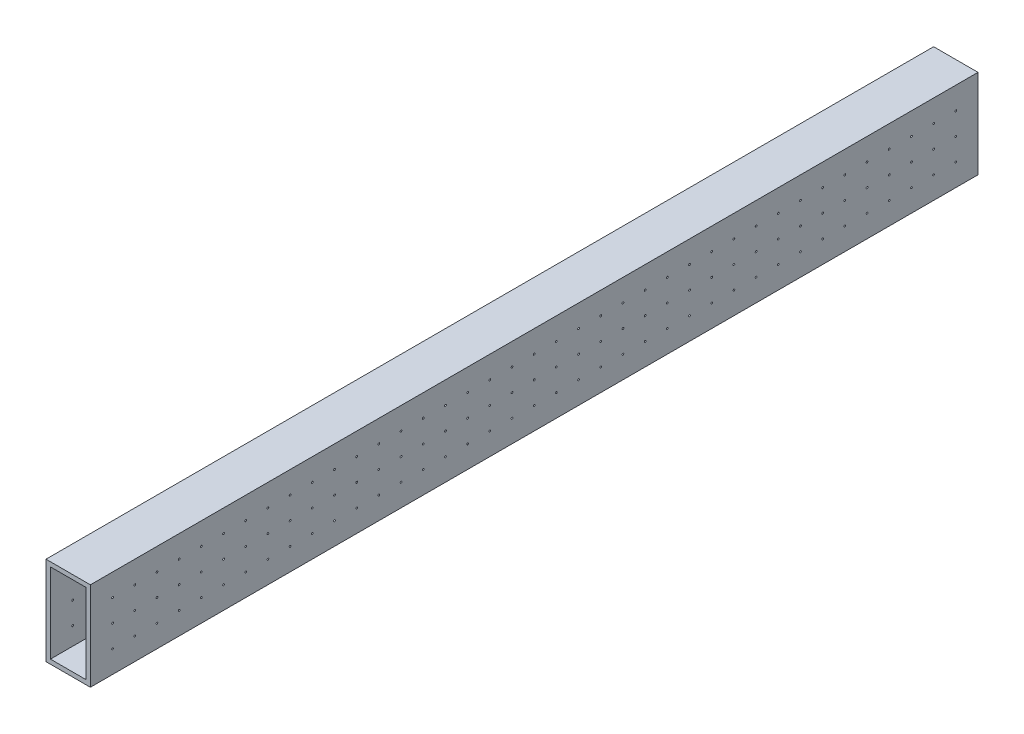
SolidWorks part; units mm, degrees
ref_plane "Front Plane" through (0, 0, 0) normal (0, 0, 1) x (1, 0, 0)
ref_plane "Top Plane" through (0, 0, 0) normal (0, 1, 0) x (1, 0, 0)
ref_plane "Right Plane" through (0, 0, 0) normal (1, 0, 0) x (0, 0, -1)
sketch "Sketch1" plane through (0, 0, 0) normal (0, 0, 1) x (1, 0, 0)
  line L1 (37.2894, 23.2383) -> (62.6894, 23.2383)
  line L2 (37.2894, 23.2383) -> (37.2894, -27.5617)
  line L3 (37.2894, -27.5617) -> (62.6894, -27.5617)
  line L4 (62.6894, 23.2383) -> (62.6894, -27.5617)
  line L5 (39.8294, 20.6983) -> (60.1494, 20.6983)
  line L6 (39.8294, 20.6983) -> (39.8294, -25.0217)
  line L7 (39.8294, -25.0217) -> (60.1494, -25.0217)
  line L8 (60.1494, 20.6983) -> (60.1494, -25.0217)
  dimension "D1" = 50.8
  dimension "D2" = 25.4
  dimension "D3" = 2.54
  dimension "D4" = 2.54
  dimension "D5" = 2.54
  dimension "D6" = 2.54
extrude "Boss-Extrude1" add sketch "Sketch1" along normal blind 508
sketch "Sketch2" plane through (37.2894, 0, 0) normal (-1, 0, 0) x (0, 0, 1)
  line L0 (0, 23.2383) -> (0, -27.5617) construction
  line L1 (508, 23.2383) -> (0, 23.2383) construction
  circle A0 centre (12.7, 10.5383) radius 0.5
  circle A1 centre (25.4, 10.5383) radius 0.5
  circle A2 centre (38.1, 10.5383) radius 0.5
  circle A3 centre (50.8, 10.5383) radius 0.5
  circle A4 centre (63.5, 10.5383) radius 0.5
  circle A5 centre (76.2, 10.5383) radius 0.5
  circle A6 centre (88.9, 10.5383) radius 0.5
  circle A7 centre (101.6, 10.5383) radius 0.5
  circle A8 centre (114.3, 10.5383) radius 0.5
  circle A9 centre (127, 10.5383) radius 0.5
  circle A10 centre (139.7, 10.5383) radius 0.5
  circle A11 centre (152.4, 10.5383) radius 0.5
  circle A12 centre (165.1, 10.5383) radius 0.5
  circle A13 centre (177.8, 10.5383) radius 0.5
  circle A14 centre (190.5, 10.5383) radius 0.5
  circle A15 centre (203.2, 10.5383) radius 0.5
  circle A16 centre (215.9, 10.5383) radius 0.5
  circle A17 centre (228.6, 10.5383) radius 0.5
  circle A18 centre (241.3, 10.5383) radius 0.5
  circle A19 centre (254, 10.5383) radius 0.5
  circle A20 centre (266.7, 10.5383) radius 0.5
  circle A21 centre (279.4, 10.5383) radius 0.5
  circle A22 centre (292.1, 10.5383) radius 0.5
  circle A23 centre (304.8, 10.5383) radius 0.5
  circle A24 centre (317.5, 10.5383) radius 0.5
  circle A25 centre (330.2, 10.5383) radius 0.5
  circle A26 centre (342.9, 10.5383) radius 0.5
  circle A27 centre (355.6, 10.5383) radius 0.5
  circle A28 centre (368.3, 10.5383) radius 0.5
  circle A29 centre (381, 10.5383) radius 0.5
  circle A30 centre (393.7, 10.5383) radius 0.5
  circle A31 centre (406.4, 10.5383) radius 0.5
  circle A32 centre (419.1, 10.5383) radius 0.5
  circle A33 centre (431.8, 10.5383) radius 0.5
  circle A34 centre (444.5, 10.5383) radius 0.5
  circle A35 centre (457.2, 10.5383) radius 0.5
  circle A36 centre (469.9, 10.5383) radius 0.5
  circle A37 centre (482.6, 10.5383) radius 0.5
  circle A38 centre (495.3, 10.5383) radius 0.5
  circle A47 centre (25.4, -2.1617) radius 0.5
  circle A48 centre (38.1, -2.1617) radius 0.5
  circle A49 centre (50.8, -2.1617) radius 0.5
  circle A50 centre (63.5, -2.1617) radius 0.5
  circle A51 centre (76.2, -2.1617) radius 0.5
  circle A52 centre (88.9, -2.1617) radius 0.5
  circle A53 centre (101.6, -2.1617) radius 0.5
  circle A54 centre (114.3, -2.1617) radius 0.5
  circle A55 centre (127, -2.1617) radius 0.5
  circle A56 centre (139.7, -2.1617) radius 0.5
  circle A57 centre (152.4, -2.1617) radius 0.5
  circle A58 centre (165.1, -2.1617) radius 0.5
  circle A59 centre (177.8, -2.1617) radius 0.5
  circle A60 centre (190.5, -2.1617) radius 0.5
  circle A61 centre (203.2, -2.1617) radius 0.5
  circle A62 centre (215.9, -2.1617) radius 0.5
  circle A63 centre (228.6, -2.1617) radius 0.5
  circle A64 centre (241.3, -2.1617) radius 0.5
  circle A65 centre (254, -2.1617) radius 0.5
  circle A66 centre (266.7, -2.1617) radius 0.5
  circle A67 centre (279.4, -2.1617) radius 0.5
  circle A68 centre (292.1, -2.1617) radius 0.5
  circle A69 centre (304.8, -2.1617) radius 0.5
  circle A70 centre (317.5, -2.1617) radius 0.5
  circle A71 centre (330.2, -2.1617) radius 0.5
  circle A72 centre (342.9, -2.1617) radius 0.5
  circle A73 centre (355.6, -2.1617) radius 0.5
  circle A74 centre (368.3, -2.1617) radius 0.5
  circle A75 centre (381, -2.1617) radius 0.5
  circle A76 centre (393.7, -2.1617) radius 0.5
  circle A77 centre (406.4, -2.1617) radius 0.5
  circle A78 centre (419.1, -2.1617) radius 0.5
  circle A79 centre (431.8, -2.1617) radius 0.5
  circle A80 centre (444.5, -2.1617) radius 0.5
  circle A81 centre (457.2, -2.1617) radius 0.5
  circle A82 centre (469.9, -2.1617) radius 0.5
  circle A83 centre (482.6, -2.1617) radius 0.5
  circle A84 centre (495.3, -2.1617) radius 0.5
  circle A93 centre (25.4, -14.8617) radius 0.5
  circle A94 centre (38.1, -14.8617) radius 0.5
  circle A95 centre (50.8, -14.8617) radius 0.5
  circle A96 centre (63.5, -14.8617) radius 0.5
  circle A97 centre (76.2, -14.8617) radius 0.5
  circle A98 centre (88.9, -14.8617) radius 0.5
  circle A99 centre (101.6, -14.8617) radius 0.5
  circle A100 centre (114.3, -14.8617) radius 0.5
  circle A101 centre (127, -14.8617) radius 0.5
  circle A102 centre (139.7, -14.8617) radius 0.5
  circle A103 centre (152.4, -14.8617) radius 0.5
  circle A104 centre (165.1, -14.8617) radius 0.5
  circle A105 centre (177.8, -14.8617) radius 0.5
  circle A106 centre (190.5, -14.8617) radius 0.5
  circle A107 centre (203.2, -14.8617) radius 0.5
  circle A108 centre (215.9, -14.8617) radius 0.5
  circle A109 centre (228.6, -14.8617) radius 0.5
  circle A110 centre (241.3, -14.8617) radius 0.5
  circle A111 centre (254, -14.8617) radius 0.5
  circle A112 centre (266.7, -14.8617) radius 0.5
  circle A113 centre (279.4, -14.8617) radius 0.5
  circle A114 centre (292.1, -14.8617) radius 0.5
  circle A115 centre (304.8, -14.8617) radius 0.5
  circle A116 centre (317.5, -14.8617) radius 0.5
  circle A117 centre (330.2, -14.8617) radius 0.5
  circle A118 centre (342.9, -14.8617) radius 0.5
  circle A119 centre (355.6, -14.8617) radius 0.5
  circle A120 centre (368.3, -14.8617) radius 0.5
  circle A121 centre (381, -14.8617) radius 0.5
  circle A122 centre (393.7, -14.8617) radius 0.5
  circle A123 centre (406.4, -14.8617) radius 0.5
  circle A124 centre (419.1, -14.8617) radius 0.5
  circle A125 centre (431.8, -14.8617) radius 0.5
  circle A126 centre (444.5, -14.8617) radius 0.5
  circle A127 centre (457.2, -14.8617) radius 0.5
  circle A128 centre (469.9, -14.8617) radius 0.5
  circle A129 centre (482.6, -14.8617) radius 0.5
  circle A130 centre (495.3, -14.8617) radius 0.5
  circle A139 centre (12.7, -2.1617) radius 0.5
  circle A140 centre (12.7, -14.8617) radius 0.5
  dimension "D1" = 1
  dimension "D2" = 12.7
  dimension "D3" = 12.7
  dimension "D4" = 39
  dimension "D5" = 3
extrude "Cut-Extrude1" cut sketch "Sketch2" against normal through all both and the other way through all
